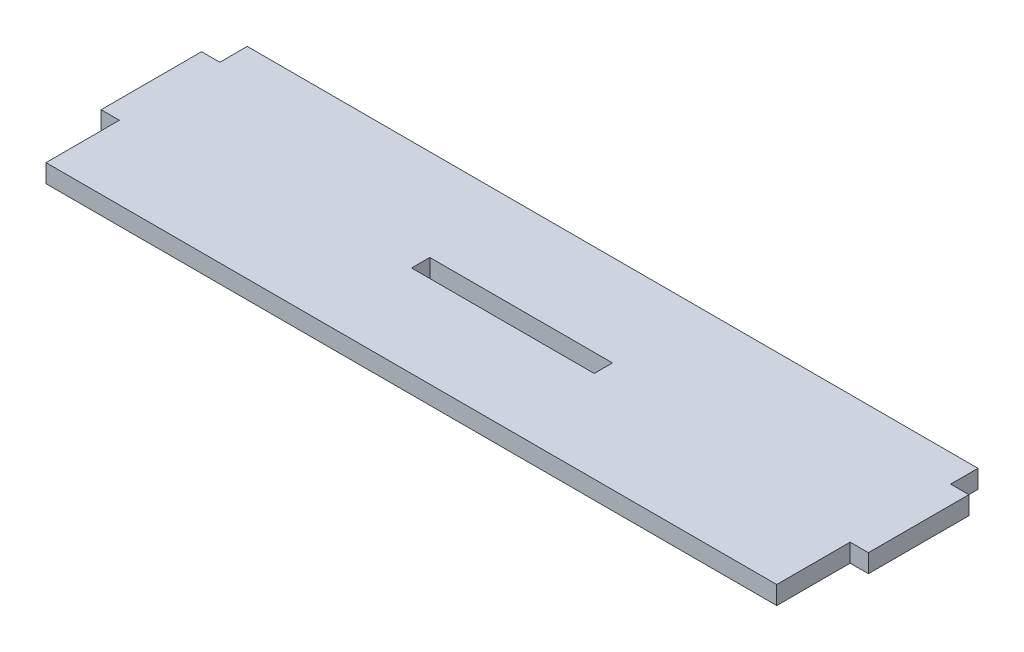
SolidWorks part; units mm, degrees
ref_plane "Front Plane" through (0, 0, 0) normal (0, 0, 1) x (1, 0, 0)
ref_plane "Top Plane" through (0, 0, 0) normal (0, 1, 0) x (1, 0, 0)
ref_plane "Right Plane" through (0, 0, 0) normal (1, 0, 0) x (0, 0, -1)
sketch "Sketch2" plane through (0, 0, 0) normal (0, 1, 0) x (1, 0, 0)
  line L0 (0, -6) -> (-4, -6)
  line L1 (0, 0) -> (160, 0)
  line L2 (0, 0) -> (0, -6)
  line L3 (0, -44.07) -> (160, -44.07)
  line L4 (160, 0) -> (160, -6)
  line L5 (-4, -6) -> (-4, -28)
  line L6 (-4, -28) -> (0, -28)
  line L7 (80, 0) -> (80, -36.6386) construction
  line L8 (164, -28) -> (160, -28)
  line L9 (164, -6) -> (164, -28)
  line L10 (160, -6) -> (164, -6)
  line L11 (0, -28) -> (0, -44.07)
  line L12 (160, -28) -> (160, -44.07)
  line L13 (8.7933, 0) -> (8.7933, -44.07) construction
  line L14 (8.7933, -22.035) -> (150.2461, -22.035) construction
  line L15 (60, -20.035) -> (60, -24.035)
  line L16 (60, -24.035) -> (100, -24.035)
  line L17 (100, -20.035) -> (100, -24.035)
  line L18 (60, -20.035) -> (100, -20.035)
  point P24 (80, -24.035)
  point P25 (100, -22.035)
  point P26 (60, -22.035)
  dimension "D1" = 168
  dimension "D2" = 44.07
  dimension "D3" = 4
  dimension "D4" = 22
  dimension "D5" = 6
  dimension "D6" = 20
  dimension "D7" = 2
extrude "Boss-Extrude1" add sketch "Sketch2" along normal blind 4
